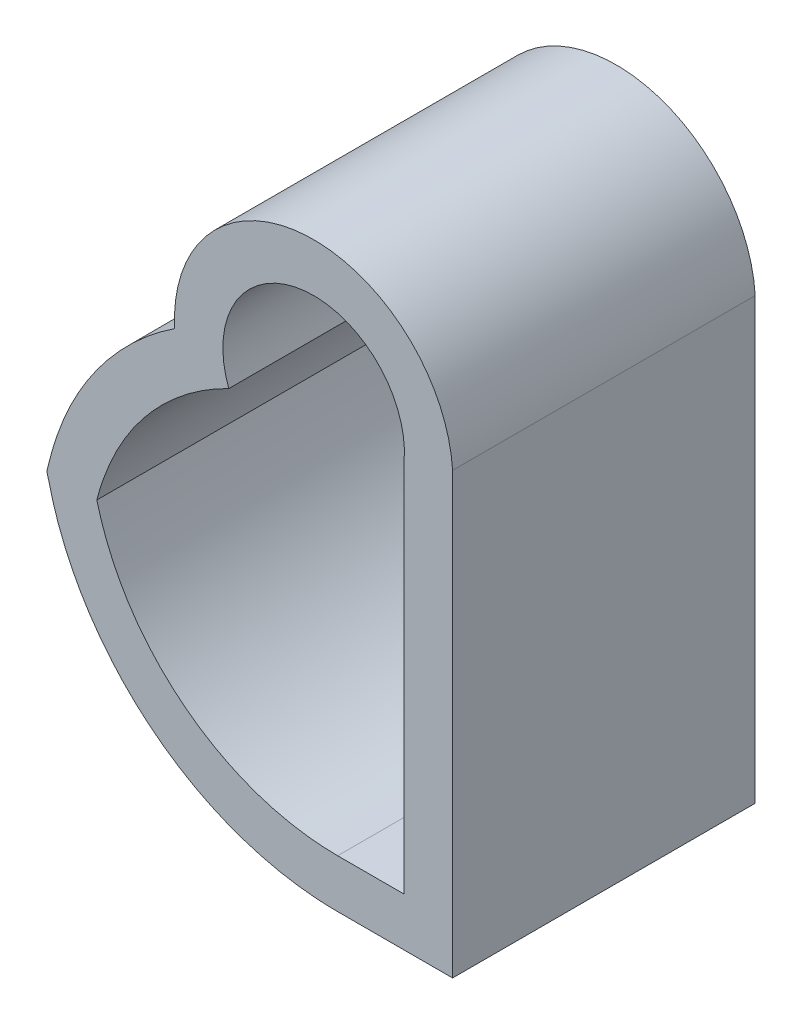
SolidWorks part; units mm, degrees
ref_plane "Front Plane" through (0, 0, 0) normal (0, 0, 1) x (1, 0, 0)
ref_plane "Top Plane" through (0, 0, 0) normal (0, 1, 0) x (1, 0, 0)
ref_plane "Right Plane" through (0, 0, 0) normal (1, 0, 0) x (0, 0, -1)
sketch "Sketch1" plane through (0, 0, 0) normal (0, 0, 1) x (1, 0, 0)
  line L0 (-75.106, 20.1) -> (-76.2046, 20.1)
  line L1 (-76.2046, 13.9) -> (-75.106, 13.9)
  line L2 (-75.106, 13.9) -> (-75.106, 20.1)
  line L3 (-75.206, 20) -> (-76.2046, 20)
  line L4 (-76.2046, 14) -> (-75.206, 14)
  line L5 (-75.206, 14) -> (-75.206, 20)
  line L6 (-75.206, 20) -> (-76.2046, 20)
  line L7 (-76.2046, 14) -> (-75.206, 14)
  line L8 (-75.206, 14) -> (-75.206, 20)
  line L9 (-74.306, 20.9) -> (-76.2046, 20.9)
  line L10 (-76.2046, 13.1) -> (-74.306, 13.1)
  line L11 (-74.306, 13.1) -> (-74.306, 20.9)
  arc A0 (-75.106, 20.1) -> (-78.0035, 19.685) centre (-76.6013, 20.2179) ccw
  arc A1 (-74.306, 20.0719) -> (-78.7513, 19.4008) centre (-76.6013, 20.2179) ccw
  arc A2 (-74.3085, 20.0371) -> (-78.7513, 19.4008) centre (-76.6013, 20.2179) ccw construction
  spline S0 degree 1 poles (-76.2046, 20.1) (-80.1841, 17) knots 0 0 1 1 construction
  spline S1 degree 1 poles (-80.1841, 17) (-76.2046, 13.9) knots 0 0 1 1 construction
  spline S2 degree 3 poles (494.3294, -3937.8938) (85.3116, -656.5034) (-34.2527, 27.0492) (-77.0811, 19.9092) (-77.2967, 19.8545) (-77.7108, 19.7125) (-77.9111, 19.625) (-78.2979, 19.4167) (-78.4848, 19.295) (-78.831, 19.0267) (-78.9923, 18.8792) (-79.2907, 18.5573) (-79.4284, 18.3817) (-79.6694, 18.0156) (-79.7743, 17.8239) (-86.6772, 2.2922) (-2.2013, -73.1505) (1523.2705, 3679.6684) knots -24.352457 -24.352457 -24.352457 -24.352457 0.125 0.125 0.25 0.25 0.375 0.375 0.5 0.5 0.625 0.625 0.75 0.75 0.875 0.875 10.435791 10.435791 10.435791 10.435791 only from (-76.2046, 20) to (-80.0808, 17)
  spline S3 degree 3 poles (3575.5826, 1637.9859) (370.616, 281.9977) (-95.0045, 50.5123) (-79.7758, 16.1792) (-79.6697, 15.9847) (-79.3047, 15.4309) (-79.0057, 15.1082) (-78.3054, 14.5664) (-77.9191, 14.3584) (-24.5163, -3.8831) (222.7156, 1118.8376) (756.5715, 3924.8984) knots -21.200111 -21.200111 -21.200111 -21.200111 0.125 0.125 0.25 0.25 0.5 0.5 0.75 0.75 32.326801 32.326801 32.326801 32.326801 only from (-80.0808, 17) to (-76.2046, 14)
  spline S4 degree 3 poles (-76.2046, 20) (-76.4263, 20) (-76.6459, 19.9817) (-77.0811, 19.9092) (-77.2967, 19.8545) (-77.7108, 19.7125) (-77.9111, 19.625) (-78.2979, 19.4167) (-78.4848, 19.295) (-78.831, 19.0267) (-78.9923, 18.8792) (-79.2907, 18.5573) (-79.4284, 18.3817) (-79.6694, 18.0156) (-79.7743, 17.8239) (-79.9524, 17.423) (-80.0259, 17.2123) (-80.0808, 17) knots 0 0 0 0 0.125 0.125 0.25 0.25 0.375 0.375 0.5 0.5 0.625 0.625 0.75 0.75 0.875 0.875 1 1 1 1
  spline S5 degree 3 poles (-80.0808, 17) (-80.0255, 16.7862) (-79.9533, 16.5793) (-79.7758, 16.1792) (-79.6697, 15.9847) (-79.3047, 15.4309) (-79.0057, 15.1082) (-78.3054, 14.5664) (-77.9191, 14.3584) (-77.0802, 14.0718) (-76.6485, 14) (-76.2046, 14) knots 0 0 0 0 0.125 0.125 0.25 0.25 0.5 0.5 0.75 0.75 1 1 1 1
  spline S6 degree 3 poles (-76.2046, 20.1) (-76.5978, 20.1) (-77.1083, 20.0256) (-77.8026, 19.7882) (-78.2615, 19.5645) (-78.9677, 19.0822) (-79.7079, 18.2793) (-80.0715, 17.4357) (-80.1841, 17) knots 0 0 0 0 0.21846 0.281267 0.406881 0.502455 0.753683 1.00491 1.00491 1.00491 1.00491
  spline S7 degree 3 poles (-80.1841, 17) (-80.0713, 16.5638) (-79.707, 15.7193) (-78.7732, 14.7069) (-77.5638, 14.051) (-76.6553, 13.9) (-76.2046, 13.9) knots -0.004875 -0.004875 -0.004875 -0.004875 0.246344 0.497562 0.748781 1 1 1 1
  spline S8 degree 1 poles (-76.2046, 20.9) (-81.0103, 17) knots 0 0 1 1 construction
  spline S9 degree 1 poles (-81.0103, 17) (-76.2046, 13.1) knots 0 0 1 1 construction
  spline S10 degree 3 poles (-76.2046, 20.9) (-76.7656, 20.9) (-77.899, 20.7023) (-79.3806, 19.8603) (-80.3131, 18.7755) (-80.7409, 17.8969) (-80.9011, 17.4214) (-80.9692, 17.1596) (-80.996, 17.0554) (-81.0103, 17) knots 0 0 0 0 0.261048 0.522096 0.783143 0.913667 0.978929 1.01156 1.044191 1.044191 1.044191 1.044191
  spline S11 degree 3 poles (-81.0103, 17) (-80.9959, 16.9442) (-80.9689, 16.8393) (-80.9004, 16.576) (-80.7417, 16.1052) (-80.3117, 15.2216) (-79.3787, 14.1377) (-77.8919, 13.2953) (-76.7639, 13.1) (-76.2046, 13.1) knots -0.043877 -0.043877 -0.043877 -0.043877 -0.011256 0.021365 0.086607 0.217092 0.478061 0.739031 1 1 1 1
  dimension "D4" = 1.5
  dimension "D5" = 0.8
  dimension "D1" = 0
  dimension "D2" = 0.1
  dimension "D3" = 0.9
extrude "Boss-Extrude1" add sketch "Sketch1" along normal blind 5
